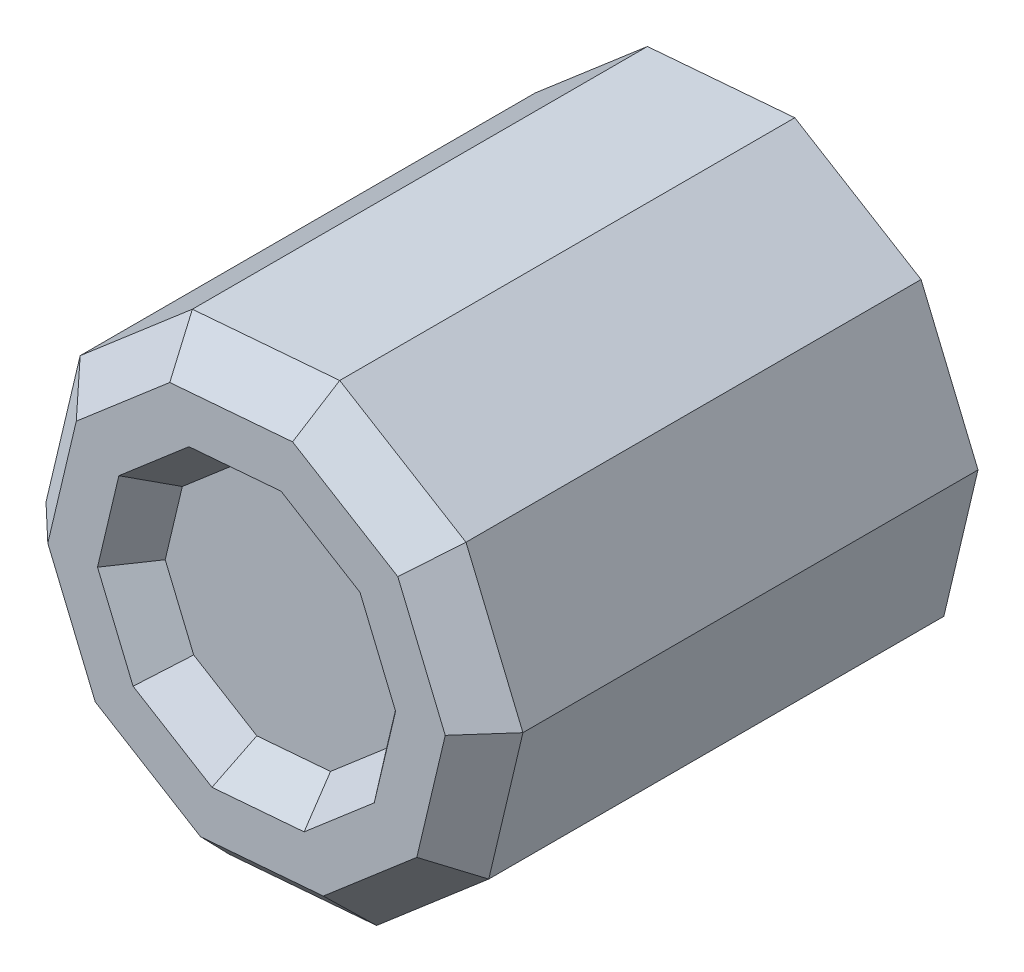
SolidWorks part; units mm, degrees
ref_plane "前视基准面" through (0, 0, 0) normal (0, 0, 1) x (1, 0, 0)
ref_plane "上视基准面" through (0, 0, 0) normal (0, 1, 0) x (1, 0, 0)
ref_plane "右视基准面" through (0, 0, 0) normal (1, 0, 0) x (0, 0, -1)
other "Configuration Table"
sketch "草图1" plane through (0, 0, 0) normal (0, 0, 1) x (1, 0, 0)
  line L1 (1.4571, 6.1382) -> (-2.4291, 5.8224)
  line L2 (-2.4291, 5.8224) -> (-5.3875, 3.2826)
  line L3 (-5.3875, 3.2826) -> (-6.288, -0.511)
  line L4 (-6.288, -0.511) -> (-4.7868, -4.1094)
  line L5 (-4.7868, -4.1094) -> (-1.4571, -6.1382)
  line L6 (-1.4571, -6.1382) -> (2.4291, -5.8224)
  line L7 (2.4291, -5.8224) -> (5.3875, -3.2826)
  line L8 (5.3875, -3.2826) -> (6.288, 0.511)
  line L9 (6.288, 0.511) -> (4.7868, 4.1094)
  line L10 (4.7868, 4.1094) -> (1.4571, 6.1382)
  circle A0 centre (0, 0) radius 3.05
  circle A1 centre (0, 0) radius 6 construction
  dimension "D1" = 6.1
  dimension "D2" = 12
extrude "凸台-拉伸1" add sketch "草图1" along normal blind 12
sketch "草图2" plane through (0, 0, 12) normal (0, 0, 1) x (1, 0, 0)
  circle A0 centre (0, 0) radius 3.0982
extrude "凸台-拉伸2" add sketch "草图2" against normal blind 2
sketch "草图3" plane through (0, 0, 10) normal (0, 0, -1) x (-1, 0, 0)
  line L1 (1.45, 2.6833) -> (1.45, -2.6833)
  circle A1 centre (0, 0) radius 3.05 construction
  circle A2 centre (0, 0) radius 3.05 construction
  arc A3 (1.45, -2.6833) -> (1.45, 2.6833) centre (0, 0) ccw
  point P1 (-3.05, 0)
  dimension "D1" = 4.5
extrude "凸台-拉伸3" add sketch "草图3" along normal blind 7
chamfer "倒角1" distance 1 angle 45 10 edges at (5.5374, 2.3102, 12) (5.8378, -1.3858, 12) (3.9083, -4.5525, 12) (0.486, -5.9803, 12) (-3.122, -5.1238, 12) (-5.5374, -2.3102, 12) (-5.8378, 1.3858, 12) (-3.9083, 4.5525, 12) (-0.486, 5.9803, 12) (3.122, 5.1238, 12)
ref_plane "基准面1" through (0, 0, 11) normal (0, 0, 1) x (1, 0, 0)
sketch "草图4" plane through (0, 0, 11) normal (0, 0, 1) x (1, 0, 0)
  line L0 (1.4571, 6.1382) -> (-1.4571, -6.1382) construction
  line L1 (0.7286, 3.0691) -> (-1.2145, 2.9112)
  line L2 (-1.2145, 2.9112) -> (-2.6937, 1.6413)
  line L3 (-2.6937, 1.6413) -> (-3.144, -0.2555)
  line L4 (-3.144, -0.2555) -> (-2.3934, -2.0547)
  line L5 (-2.3934, -2.0547) -> (-0.7286, -3.0691)
  line L6 (-0.7286, -3.0691) -> (1.2145, -2.9112)
  line L7 (1.2145, -2.9112) -> (2.6937, -1.6413)
  line L8 (2.6937, -1.6413) -> (3.144, 0.2555)
  line L9 (3.144, 0.2555) -> (2.3934, 2.0547)
  line L10 (2.3934, 2.0547) -> (0.7286, 3.0691)
  circle A0 centre (0, 0) radius 3 construction
  dimension "D1" = 6
sketch "草图5" plane through (0, 0, 12) normal (0, 0, 1) x (1, 0, 0)
  line L1 (0.9107, 3.8364) -> (-1.5182, 3.639)
  line L2 (-1.5182, 3.639) -> (-3.3672, 2.0516)
  line L3 (-3.3672, 2.0516) -> (-3.93, -0.3194)
  line L4 (-3.93, -0.3194) -> (-2.9917, -2.5684)
  line L5 (-2.9917, -2.5684) -> (-0.9107, -3.8364)
  line L6 (-0.9107, -3.8364) -> (1.5182, -3.639)
  line L7 (1.5182, -3.639) -> (3.3672, -2.0516)
  line L8 (3.3672, -2.0516) -> (3.93, 0.3194)
  line L9 (3.93, 0.3194) -> (2.9917, 2.5684)
  line L10 (2.9917, 2.5684) -> (0.9107, 3.8364)
  circle A0 centre (0, 0) radius 3.75 construction
loft "切除-放样1" cut profiles "草图5", "草图4"
sketch "草图6" plane through (0, 0, 3) normal (0, 0, -1) x (-1, 0, 0)
  circle A0 centre (0, 0) radius 3.05
extrude "切除-拉伸2" cut sketch "草图6" against normal blind 7
sketch "草图7" plane through (0, 0, 0) normal (0, 0, -1) x (-1, 0, 0)
  circle A0 centre (0, 0) radius 3.05
  circle A1 centre (0, 0) radius 3
  dimension "D1" = 6
extrude "凸台-拉伸4" add sketch "草图7" against normal blind 10
sketch "草图8" plane through (0, 0, 0) normal (0, 0, -1) x (-1, 0, 0)
  line L1 (2.4291, 5.8224) -> (-1.4571, 6.1382)
  line L2 (-1.4571, 6.1382) -> (-4.7868, 4.1094)
  line L3 (-4.7868, 4.1094) -> (-6.288, 0.511)
  line L4 (-6.288, 0.511) -> (-5.3875, -3.2826)
  line L5 (-5.3875, -3.2826) -> (-2.4291, -5.8224)
  line L6 (-2.4291, -5.8224) -> (1.4571, -6.1382)
  line L7 (1.4571, -6.1382) -> (4.7868, -4.1094)
  line L8 (4.7868, -4.1094) -> (6.288, -0.511)
  line L9 (6.288, -0.511) -> (5.3875, 3.2826)
  line L10 (5.3875, 3.2826) -> (2.4291, 5.8224)
  circle A0 centre (0, 0) radius 3
  circle A1 centre (0, 0) radius 6 construction
extrude "凸台-拉伸5" add sketch "草图8" along normal blind 1
